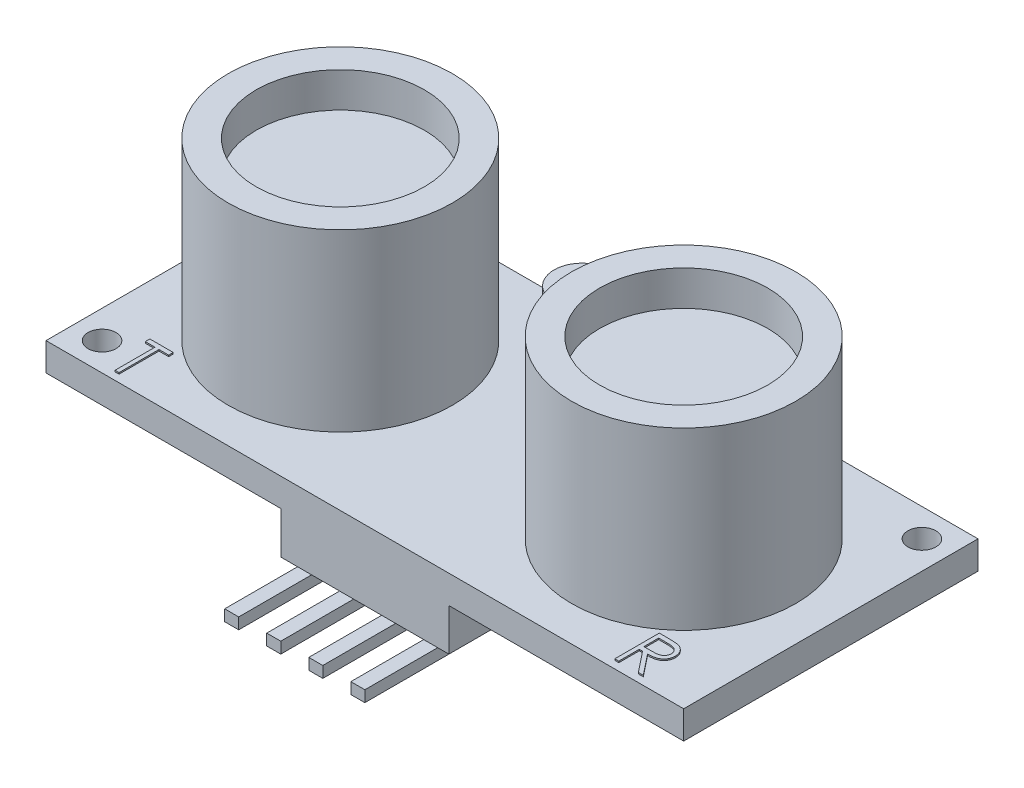
SolidWorks part; units mm, degrees
ref_plane "Front Plane" through (0, 0, 0) normal (0, 0, 1) x (1, 0, 0)
ref_plane "Top Plane" through (0, 0, 0) normal (0, 1, 0) x (1, 0, 0)
ref_plane "Right Plane" through (0, 0, 0) normal (1, 0, 0) x (0, 0, -1)
sketch "Sketch2" plane through (0, 0, 0) normal (0, 1, 0) x (1, 0, 0)
  line L0 (-22.75, 0) -> (-22.75, 25.4681) construction
  line L1 (0, 0) -> (-45.5, 0)
  line L2 (0, 0) -> (0, 21)
  line L3 (0, 21) -> (-45.5, 21)
  line L4 (-45.5, 0) -> (-45.5, 21)
  dimension "D1" = 21
  dimension "D2" = 45.5
extrude "Boss-Extrude2" add sketch "Sketch2" along normal blind 2
sketch "Sketch4" plane through (0, 2, 0) normal (0, 1, 0) x (1, 0, 0)
  line L0 (-45.5, 21) -> (-45.5, 0) construction
  line L1 (0, 21) -> (-45.5, 21) construction
  line L2 (-22.75, 21) -> (-22.75, -1.3189) construction
  circle A0 centre (-35, 10.5) radius 8
  circle A1 centre (-10.5, 10.5) radius 8
  dimension "D1" = 16
  dimension "D2" = 10.5
  dimension "D3" = 10.5
extrude "Boss-Extrude3" add sketch "Sketch4" along normal blind 12.5
sketch "Sketch5" plane through (0, 14.5, 0) normal (0, 1, 0) x (1, 0, 0)
  circle A0 centre (-35, 10.5) radius 6
  circle A1 centre (-10.5, 10.5) radius 6
  dimension "D1" = 12
  dimension "D2" = 12
extrude "Cut-Extrude1" cut sketch "Sketch5" against normal blind 2.5
sketch "Sketch6" plane through (0, 2, 0) normal (0, 1, 0) x (1, 0, 0)
  line L0 (-22.75, 21) -> (-22.75, -3.4225) construction
  line L1 (0, 21) -> (-45.5, 21) construction
  line L2 (-25.75, 18.5) -> (-19.75, 18.5) construction
  line L9 (-25.75, 18.5) -> (-19.75, 18.5) construction
  line L10 (-25.75, 20.494) -> (-19.75, 20.494)
  line L11 (-25.75, 16.506) -> (-19.75, 16.506)
  arc A0 (-25.75, 20.494) -> (-25.75, 16.506) centre (-25.75, 18.5) ccw
  arc A1 (-19.75, 16.506) -> (-19.75, 20.494) centre (-19.75, 18.5) ccw
  point P4 (-22.75, 18.5)
  point P13 (-22.75, 18.5)
  dimension "D4" = 6
  dimension "D1" = 1.994
  dimension "D3" = 2.5
extrude "Boss-Extrude5" add sketch "Sketch6" along normal blind 4
sketch "Sketch7" plane through (0, 0, 0) normal (0, -1, 0) x (1, 0, 0)
  line L0 (-22.75, -21) -> (-22.75, 2.8689) construction
  line L1 (0, -21) -> (-45.5, -21) construction
  line L2 (7.975, 0) -> (-7.975, 0) construction
  line L3 (-28.75, 0) -> (-16.75, 0)
  line L4 (-22.75, 0) -> (-22.75, -3)
  line L5 (-28.75, -3) -> (-16.75, -3)
  line L6 (-16.75, 0) -> (-16.75, -3)
  line L7 (-28.75, 0) -> (-28.75, -3)
  line M8 (0, 0) -> (-45.5, 0)
  dimension "D1" = 6
  dimension "D2" = 3
extrude "Boss-Extrude6" add sketch "Sketch7" along normal blind 3 contours L6 L4 L5 M8 | L3 L7 L5 L4
sketch "Sketch8" plane through (0, -3, 0) normal (0, -1, 0) x (1, 0, 0)
  line L0 (-16.75, -1.5) -> (-28.75, -1.5) construction
  line L1 (-16.75, 0) -> (-16.75, -3) construction
  line L2 (-28.75, 0) -> (-28.75, -3) construction
  line L3 (-22.75, -1.5) -> (-22.75, -3) construction
  line L4 (-28.75, -3) -> (-16.75, -3) construction
  line L5 (-22.75, -3) -> (-22.75, 0) construction
  line L6 (10.175, 0) -> (-10.175, 0) construction
  line L7 (-24.75, -2) -> (-23.75, -2)
  line L8 (-20.75, -1) -> (-21.75, -1)
  line L9 (-20.75, -1) -> (-20.75, -2)
  line L10 (-20.75, -2) -> (-21.75, -2)
  line L11 (-21.75, -1) -> (-21.75, -2)
  line L12 (-20.75, -1) -> (-21.75, -2) construction
  line L13 (-20.75, -2) -> (-21.75, -1) construction
  line L14 (-17.75, -1) -> (-18.75, -1)
  line L15 (-17.75, -1) -> (-17.75, -2)
  line L16 (-17.75, -2) -> (-18.75, -2)
  line L17 (-18.75, -1) -> (-18.75, -2)
  line L18 (-17.75, -1) -> (-18.75, -2) construction
  line L19 (-17.75, -2) -> (-18.75, -1) construction
  line L20 (-24.75, -1) -> (-24.75, -2)
  line L21 (-23.75, -1) -> (-23.75, -2)
  line L22 (-24.75, -1) -> (-23.75, -1)
  line L23 (-27.75, -1) -> (-26.75, -1)
  line L24 (-27.75, -1) -> (-27.75, -2)
  line L25 (-27.75, -2) -> (-26.75, -2)
  line L26 (-26.75, -1) -> (-26.75, -2)
  point P10 (-21.25, -1.5)
  point P18 (-18.25, -1.5)
  dimension "D1" = 1.5
  dimension "D2" = 1
  dimension "D3" = 1
  dimension "D4" = 3
  dimension "D5" = 1
  dimension "D6" = 1
extrude "Boss-Extrude7" add sketch "Sketch8" along normal blind 1
sketch "Sketch9" plane through (0, 0, -1) normal (0, 0, 1) x (1, 0, 0)
sketch "Sketch10" plane through (0, 0, -1) normal (0, 0, 1) x (1, 0, 0)
  line L0 (-18.75, -4) -> (-18.75, -3) construction
  line L1 (-17.75, -4) -> (-18.75, -4)
  line L2 (-17.75, -4) -> (-17.75, -3.2)
  line L3 (-17.75, -3.2) -> (-18.75, -3.2)
  line L4 (-18.75, -4) -> (-18.75, -3.2)
  line L5 (-21.75, -4) -> (-21.75, -3) construction
  line L6 (-20.75, -4) -> (-21.75, -4)
  line L7 (-20.75, -4) -> (-20.75, -3.2)
  line L8 (-20.75, -3.2) -> (-21.75, -3.2)
  line L9 (-21.75, -4) -> (-21.75, -3.2)
  line L10 (-24.75, -4) -> (-24.75, -3) construction
  line L11 (-23.75, -4) -> (-24.75, -4)
  line L12 (-23.75, -4) -> (-23.75, -3.2)
  line L13 (-23.75, -3.2) -> (-24.75, -3.2)
  line L14 (-24.75, -4) -> (-24.75, -3.2)
  line L15 (-27.75, -4) -> (-27.75, -3) construction
  line L16 (-26.75, -4) -> (-27.75, -4)
  line L17 (-26.75, -4) -> (-26.75, -3.2)
  line L18 (-26.75, -3.2) -> (-27.75, -3.2)
  line L19 (-27.75, -4) -> (-27.75, -3.2)
  dimension "D1" = 0.8
extrude "Boss-Extrude8" add sketch "Sketch10" along normal blind 6
sketch "Sketch11" plane through (0, 0, 0) normal (0, -1, 0) x (1, 0, 0)
  line L0 (0, -21) -> (-45.5, -21) construction
  line L2 (0, 0) -> (0, -21) construction
  line L3 (-45.5, 0) -> (-28.75, 0) construction
  line L4 (-45.5, -21) -> (-45.5, 0) construction
  circle A0 centre (-2, -19) radius 1
  circle A1 centre (-43.5, -2) radius 1
  dimension "D1" = 2
  dimension "D4" = 2
  dimension "D5" = 2
  dimension "D2" = 2
  dimension "D3" = 2
  dimension "D6" = 2
extrude "Cut-Extrude2" cut sketch "Sketch11" against normal through all
sketch "Sketch15" plane through (0, 2, 0) normal (0, 1, 0) x (1, 0, 0)
  line L0 (-45.5, 0.5309) -> (0, 0.5309) construction
  line L1 (-45.5, 21) -> (-45.5, 0) construction
  line L2 (0, 0) -> (0, 21) construction
  text T0 "   T                            R"
extrude "Boss-Extrude10" add sketch "Sketch15" along normal blind 0.1
